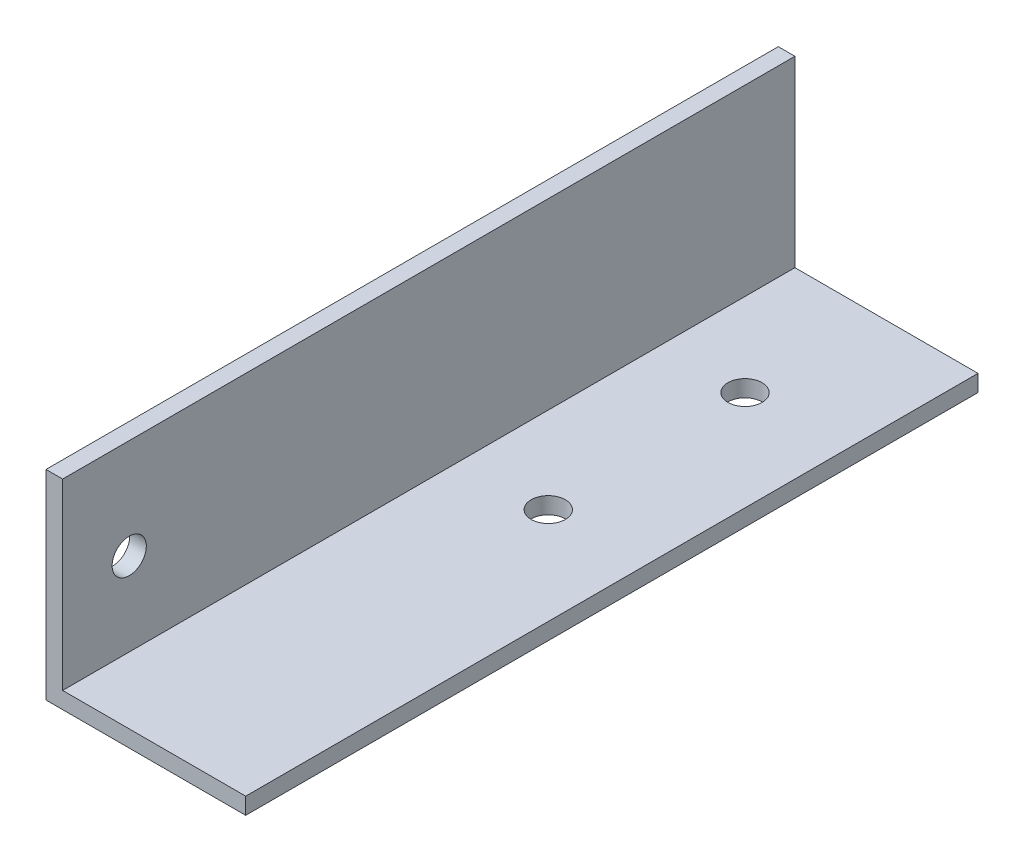
SolidWorks part; units mm, degrees
material "6061-T6 (SS)"
ref_plane "Front Plane" through (0, 0, 0) normal (0, 0, 1) x (1, 0, 0)
ref_plane "Top Plane" through (0, 0, 0) normal (0, 1, 0) x (1, 0, 0)
ref_plane "Right Plane" through (0, 0, 0) normal (1, 0, 0) x (0, 0, -1)
sketch "Sketch1" plane through (0, 0, 0) normal (0, 0, 1) x (1, 0, 0)
  line L0 (0, 0) -> (0, 19.05)
  line L1 (0, 19.05) -> (1.5875, 19.05)
  line L2 (1.5875, 19.05) -> (1.5875, 1.5875)
  line L3 (1.5875, 1.5875) -> (19.05, 1.5875)
  line L4 (19.05, 1.5875) -> (19.05, 0)
  line L5 (19.05, 0) -> (0, 0)
  dimension "D1" = 19.05
  dimension "D2" = 1.5875
extrude "Boss-Extrude1" add sketch "Sketch1" along normal blind 69.85
hole_wizard "#4 Clearance Hole1" positions "Sketch3" profile "Sketch2" hole size "#4" standard "ANSI Inch" end condition through all
sketch "Sketch3" plane through (1.5875, 0, 0) normal (1, 0, 0) x (0, 0, -1)
  line L0 (-69.85, 1.5875) -> (-69.85, 19.05) construction
  line L1 (-69.85, 19.05) -> (0, 19.05) construction
  point P0 (-63.5, 9.525)
  dimension "D1" = 6.35
  dimension "D2" = 9.525
sketch "Sketch2" plane through (1.5875, 9.525, 63.5) normal (0, 1, 0) x (0, 0, -1)
  line L0 (0, 0) -> (0, 1.5875)
  line L1 (0, 1.5875) -> (1.6319, 1.5875)
  line L2 (1.6319, 1.5875) -> (1.6319, 0)
  line L5 (1.6319, 0) -> (0, 0)
  line L11 (0, -6.35) -> (0, 107.95) construction
  dimension "Thru Hole Dia." = 3.2639
  dimension "Thru Hole Depth" = 1.5875
hole_wizard "#4 Clearance Hole2" positions "Sketch5" profile "Sketch4" hole size "#4" standard "ANSI Inch" end condition through all
sketch "Sketch5" plane through (0, 1.5875, 0) normal (0, 1, 0) x (1, 0, 0)
  line L0 (19.05, -69.85) -> (19.05, 0) construction
  line L3 (19.05, 0) -> (1.5875, 0) construction
  point P0 (9.525, -12.7)
  point P2 (9.8079, -31.75)
  dimension "D1" = 9.525
  dimension "D2" = 12.7
  dimension "D3" = 19.05
sketch "Sketch4" plane through (9.525, 1.5875, 12.7) normal (1, 0, 0) x (0, 0, 1)
  line L0 (0, 0) -> (0, 1.5875)
  line L1 (0, 1.5875) -> (1.6319, 1.5875)
  line L2 (1.6319, 1.5875) -> (1.6319, 0)
  line L5 (1.6319, 0) -> (0, 0)
  line L11 (0, -6.35) -> (0, 107.95) construction
  dimension "Thru Hole Dia." = 3.2639
  dimension "Thru Hole Depth" = 1.5875
